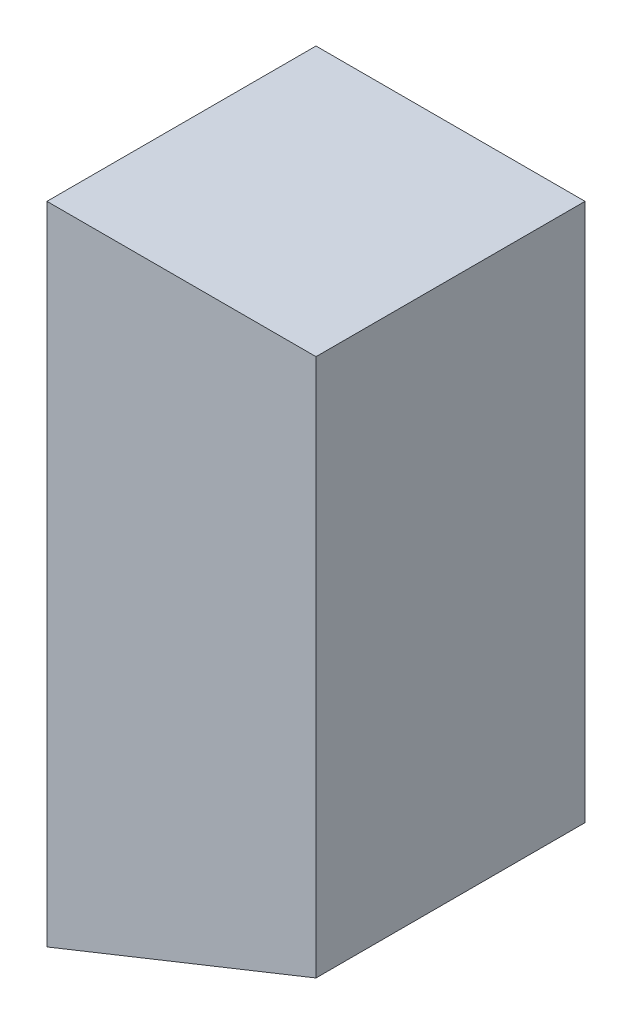
SolidWorks part; units mm, degrees
ref_plane "Alzado" through (0, 0, 0) normal (0, 0, 1) x (1, 0, 0)
ref_plane "Planta" through (0, 0, 0) normal (0, 1, 0) x (1, 0, 0)
ref_plane "Vista lateral" through (0, 0, 0) normal (1, 0, 0) x (0, 0, -1)
sketch "Croquis1" plane through (0, 0, 0) normal (0, 0, 1) x (1, 0, 0)
  line L1 (0, 0) -> (0.25, 0)
  line L2 (0, 0) -> (0, -0.6)
  line L4 (0.25, 0) -> (0.25, -0.5)
  line L5 (0, -0.6) -> (0.25, -0.5)
  dimension "D1" = 0.25
  dimension "D2" = 0.5
  dimension "D3" = 0.6
extrude "Saliente-Extruir1" add sketch "Croquis1" along normal blind 0.25
